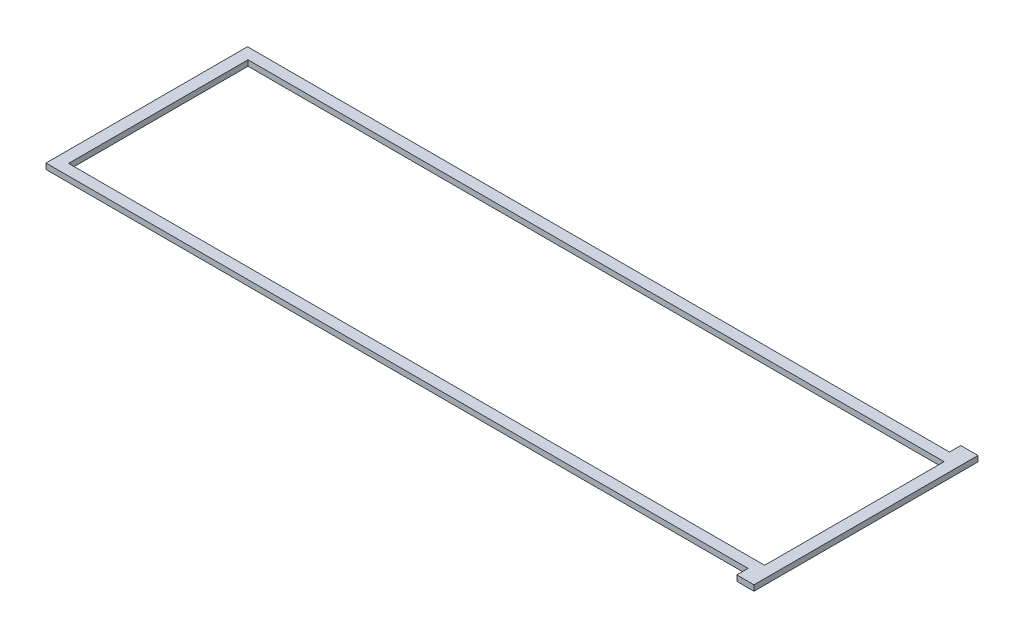
SolidWorks part; units mm, degrees
ref_plane "Front" through (0, 0, 0) normal (0, 0, 1) x (1, 0, 0)
ref_plane "Top" through (0, 0, 0) normal (0, 1, 0) x (1, 0, 0)
ref_plane "Right" through (0, 0, 0) normal (1, 0, 0) x (0, 0, -1)
sketch "Sketch1" plane through (0, 0, 0) normal (0, 1, 0) x (1, 0, 0)
  line L1 (-203.2, -63.2238) -> (203.2, -63.2238)
  line L2 (-203.2, -63.2238) -> (-203.2, 63.2238)
  line L3 (-203.2, 63.2238) -> (203.2, 63.2238)
  line L4 (203.2, -63.2238) -> (203.2, 63.2238)
  line L5 (-203.2, -63.2238) -> (203.2, 63.2238) construction
  line L6 (-203.2, 63.2238) -> (203.2, -63.2238) construction
  line L7 (-203.2, 63.2238) -> (193.675, 63.2238)
  line L8 (-203.2, 63.2238) -> (-203.2, 56.8484)
  line L9 (-203.2, 56.8484) -> (193.675, 56.8484)
  line L10 (193.675, 63.2238) -> (193.675, 56.8484)
  line L11 (-203.2, -63.2238) -> (193.675, -63.2238)
  line L12 (-203.2, -63.2238) -> (-203.2, -56.8484)
  line L13 (-203.2, -56.8484) -> (193.675, -56.8484)
  line L14 (193.675, -63.2238) -> (193.675, -56.8484)
  line L15 (-196.85, -50.8508) -> (196.85, -50.8508)
  line L16 (-196.85, -50.8508) -> (-196.85, 50.8)
  line L17 (-196.85, 50.8) -> (196.85, 50.8)
  line L18 (196.85, -50.8508) -> (196.85, 50.8)
  point P0 (0, 0)
  point P12 (0, 0)
extrude "Boss-Extrude1" add sketch "Sketch1" along normal blind 3.175 contours L14 L1 L4 L3 L10 L9 L2 L13 L18 L15 L16 L17
ref_plane "Plane1" through (0, 3.175, 0) normal (0, 1, 0) x (1, 0, 0)
sketch "Sketch2" plane through (0, 3.175, 0) normal (0, 1, 0) x (1, 0, 0)
  line L17 (193.5734, -56.95) -> (193.5734, -63.3254)
  line L18 (193.5734, -63.3254) -> (203.3016, -63.3254)
  line L19 (203.3016, -63.3254) -> (203.3016, 63.3254)
  line L20 (203.3016, 63.3254) -> (193.5734, 63.3254)
  line L21 (193.5734, 63.3254) -> (193.5734, 56.95)
  line L22 (193.5734, 56.95) -> (-203.3016, 56.95)
  line L23 (-203.3016, 56.95) -> (-203.3016, -56.95)
  line L24 (-203.3016, -56.95) -> (193.5734, -56.95)
  line L25 (193.5734, -56.95) -> (193.5734, -63.3254)
  line L26 (193.5734, -63.3254) -> (203.3016, -63.3254)
  line L27 (203.3016, -63.3254) -> (203.3016, 63.3254)
  line L28 (203.3016, 63.3254) -> (193.5734, 63.3254)
  line L29 (193.5734, 63.3254) -> (193.5734, 56.95)
  line L30 (193.5734, 56.95) -> (-203.3016, 56.95)
  line L31 (-203.3016, 56.95) -> (-203.3016, -56.95)
  line L32 (-203.3016, -56.95) -> (193.5734, -56.95)
  line L39 (196.7484, -50.7492) -> (196.7484, 50.6984)
  line L40 (-196.7484, -50.7492) -> (196.7484, -50.7492)
  line L41 (-196.7484, 50.6984) -> (-196.7484, -50.7492)
  line L42 (196.7484, 50.6984) -> (-196.7484, 50.6984)
  line L43 (196.7484, -50.7492) -> (196.7484, 50.6984)
  line L44 (-196.7484, -50.7492) -> (196.7484, -50.7492)
  line L45 (-196.7484, 50.6984) -> (-196.7484, -50.7492)
  line L46 (196.7484, 50.6984) -> (-196.7484, 50.6984)
  dimension "D1" = 0.1016
  dimension "D2" = 0.1016
extrude "Boss-Extrude2" add sketch "Sketch2" against normal blind 3.175
ref_plane "Plane2" [suppressed] through (0, 3.175, 0) normal (0, 1, 0) x (1, 0, 0)
sketch "Sketch3" [suppressed] plane through (0, 3.175, 0) normal (0, 1, 0) x (1, 0, 0)
  line L16 (193.5734, -66.0876) -> (193.5734, -72.463)
  line L17 (193.5734, -72.463) -> (203.3016, -72.463)
  line L18 (203.3016, -72.463) -> (203.3016, 72.463)
  line L19 (203.3016, 72.463) -> (193.5734, 72.463)
  line L20 (193.5734, 72.463) -> (193.5734, 66.0876)
  line L21 (193.5734, 66.0876) -> (-203.3016, 66.0876)
  line L22 (-203.3016, 66.0876) -> (-203.3016, -66.0876)
  line L23 (-203.3016, -66.0876) -> (193.5734, -66.0876)
  line L24 (193.5734, -66.0876) -> (193.5734, -72.463)
  line L25 (193.5734, -72.463) -> (203.3016, -72.463)
  line L26 (203.3016, -72.463) -> (203.3016, 72.463)
  line L27 (203.3016, 72.463) -> (193.5734, 72.463)
  line L28 (193.5734, 72.463) -> (193.5734, 66.0876)
  line L29 (193.5734, 66.0876) -> (-203.3016, 66.0876)
  line L30 (-203.3016, 66.0876) -> (-203.3016, -66.0876)
  line L31 (-203.3016, -66.0876) -> (193.5734, -66.0876)
  line L38 (196.7484, -50.7492) -> (196.7484, 50.6984)
  line L39 (-196.7484, -50.7492) -> (196.7484, -50.7492)
  line L40 (-196.7484, 50.6984) -> (-196.7484, -50.7492)
  line L41 (196.7484, 50.6984) -> (-196.7484, 50.6984)
  line L42 (196.7484, -50.7492) -> (196.7484, 50.6984)
  line L43 (-196.7484, -50.7492) -> (196.7484, -50.7492)
  line L44 (-196.7484, 50.6984) -> (-196.7484, -50.7492)
  line L45 (196.7484, 50.6984) -> (-196.7484, 50.6984)
  dimension "D1" = 0.1016
  dimension "D2" = 0.1016
extrude "Boss-Extrude3" [suppressed] add sketch "Sketch3" against normal blind 3.175
ref_plane "Plane3" [suppressed] through (0, 3.175, 0) normal (0, 1, 0) x (1, 0, 0)
sketch "Sketch4" [suppressed] plane through (0, 3.175, 0) normal (0, 1, 0) x (1, 0, 0)
  line L16 (193.5734, -61.5188) -> (193.5734, -67.8942)
  line L17 (193.5734, -67.8942) -> (203.3016, -67.8942)
  line L18 (203.3016, -67.8942) -> (203.3016, 67.8942)
  line L19 (203.3016, 67.8942) -> (193.5734, 67.8942)
  line L20 (193.5734, 67.8942) -> (193.5734, 61.5188)
  line L21 (193.5734, 61.5188) -> (-203.3016, 61.5188)
  line L22 (-203.3016, 61.5188) -> (-203.3016, -61.5188)
  line L23 (-203.3016, -61.5188) -> (193.5734, -61.5188)
  line L24 (193.5734, -61.5188) -> (193.5734, -67.8942)
  line L25 (193.5734, -67.8942) -> (203.3016, -67.8942)
  line L26 (203.3016, -67.8942) -> (203.3016, 67.8942)
  line L27 (203.3016, 67.8942) -> (193.5734, 67.8942)
  line L28 (193.5734, 67.8942) -> (193.5734, 61.5188)
  line L29 (193.5734, 61.5188) -> (-203.3016, 61.5188)
  line L30 (-203.3016, 61.5188) -> (-203.3016, -61.5188)
  line L31 (-203.3016, -61.5188) -> (193.5734, -61.5188)
  line L38 (196.7484, -50.7492) -> (196.7484, 50.6984)
  line L39 (-196.7484, -50.7492) -> (196.7484, -50.7492)
  line L40 (-196.7484, 50.6984) -> (-196.7484, -50.7492)
  line L41 (196.7484, 50.6984) -> (-196.7484, 50.6984)
  line L42 (196.7484, -50.7492) -> (196.7484, 50.6984)
  line L43 (-196.7484, -50.7492) -> (196.7484, -50.7492)
  line L44 (-196.7484, 50.6984) -> (-196.7484, -50.7492)
  line L45 (196.7484, 50.6984) -> (-196.7484, 50.6984)
  dimension "D1" = 0.1016
  dimension "D2" = 0.1016
extrude "Boss-Extrude4" [suppressed] add sketch "Sketch4" against normal blind 3.175
